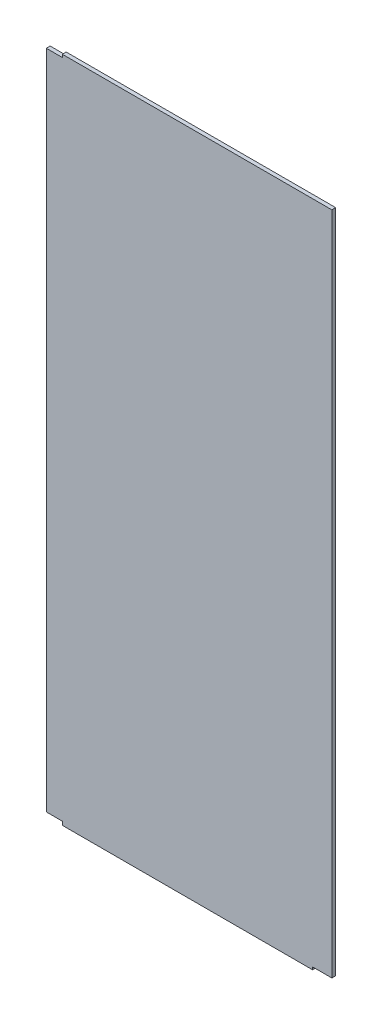
SolidWorks part; units mm, degrees
ref_plane "Alzado" through (0, 0, 0) normal (0, 0, 1) x (1, 0, 0)
ref_plane "Planta" through (0, 0, 0) normal (0, 1, 0) x (1, 0, 0)
ref_plane "Vista lateral" through (0, 0, 0) normal (1, 0, 0) x (0, 0, -1)
sketch "Croquis1" plane through (0, 0, 0) normal (0, 0, 1) x (1, 0, 0)
  line L1 (-224.4432, 296.1316) -> (-14.2432, 296.1316)
  line L2 (-236.9432, 293.9316) -> (-236.9432, -221.8684)
  line L3 (-224.4432, -224.6684) -> (-29.2432, -224.6684)
  line L4 (-14.2432, 296.1316) -> (-14.2432, -222.6684)
  line L6 (-236.9432, 293.9316) -> (-224.4432, 293.9316)
  line L7 (-224.4432, 293.9316) -> (-224.4432, 296.1316)
  line L8 (-224.4432, -224.6684) -> (-224.4432, -221.8684)
  line L9 (-224.4432, -221.8684) -> (-236.9432, -221.8684)
  line L12 (-29.2432, -224.6684) -> (-29.2432, -222.6684)
  line L13 (-29.2432, -222.6684) -> (-14.2432, -222.6684)
  dimension "D1" = 520.8
  dimension "D2" = 222.7
  dimension "D3" = 2.2
  dimension "D5" = 12.5
  dimension "D7" = 2.8
  dimension "D9" = 12.5
  dimension "D11" = 2
  dimension "D12" = 15
extrude "Saliente-Extruir1" add sketch "Croquis1" along normal blind 3
